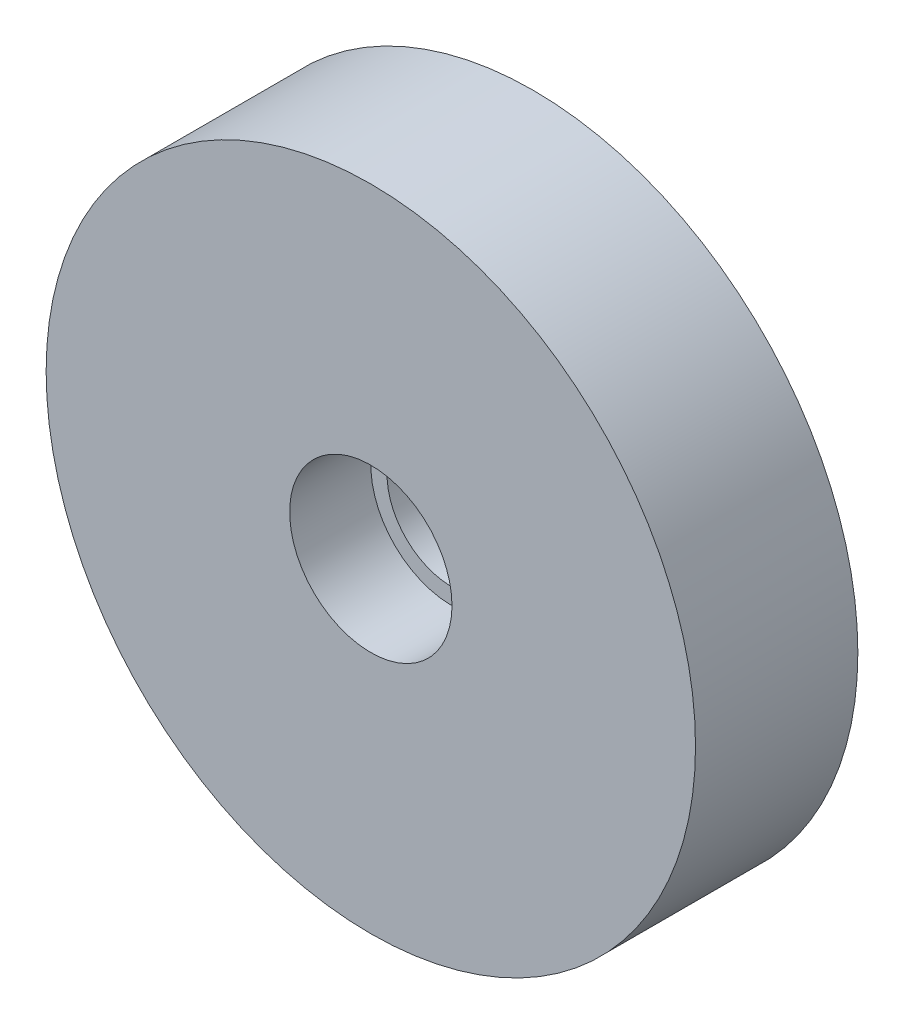
SolidWorks part; units mm, degrees
ref_plane "Plan de face" through (0, 0, 0) normal (0, 0, 1) x (1, 0, 0)
ref_plane "Plan de dessus" through (0, 0, 0) normal (0, 1, 0) x (1, 0, 0)
ref_plane "Plan de droite" through (0, 0, 0) normal (1, 0, 0) x (0, 0, -1)
sketch "Esquisse1" plane through (0, 0, 0) normal (0, 0, 1) x (1, 0, 0)
  circle A0 centre (0, 280) radius 20
extrude "Boss.-Extru.1" add sketch "Esquisse1" along normal blind 10
sketch "Esquisse2" plane through (0, 0, 10) normal (0, 0, 1) x (1, 0, 0)
  circle A0 centre (0, 280) radius 4 construction
  circle A1 centre (0, 280) radius 4
extrude "Enlèv. mat.-Extru.1" cut sketch "Esquisse2" against normal through all
sketch "Esquisse3" plane through (0, 0, 10) normal (0, 0, 1) x (1, 0, 0)
  circle A0 centre (0, 280) radius 5
extrude "Enlèv. mat.-Extru.2" cut sketch "Esquisse3" against normal blind 5
sketch "Esquisse4" plane through (0, 0, 0) normal (0, 0, -1) x (-1, 0, 0)
  circle A0 centre (0, 280) radius 12 construction
  circle A1 centre (0, 280) radius 12
extrude "Boss.-Extru.2" add sketch "Esquisse4" along normal blind 5
sketch "Esquisse5" plane through (0, 0, -5) normal (0, 0, -1) x (-1, 0, 0)
  circle A0 centre (0, 280) radius 4 construction
  circle A1 centre (0, 280) radius 4
extrude "Enlèv. mat.-Extru.6" cut sketch "Esquisse5" against normal through all
